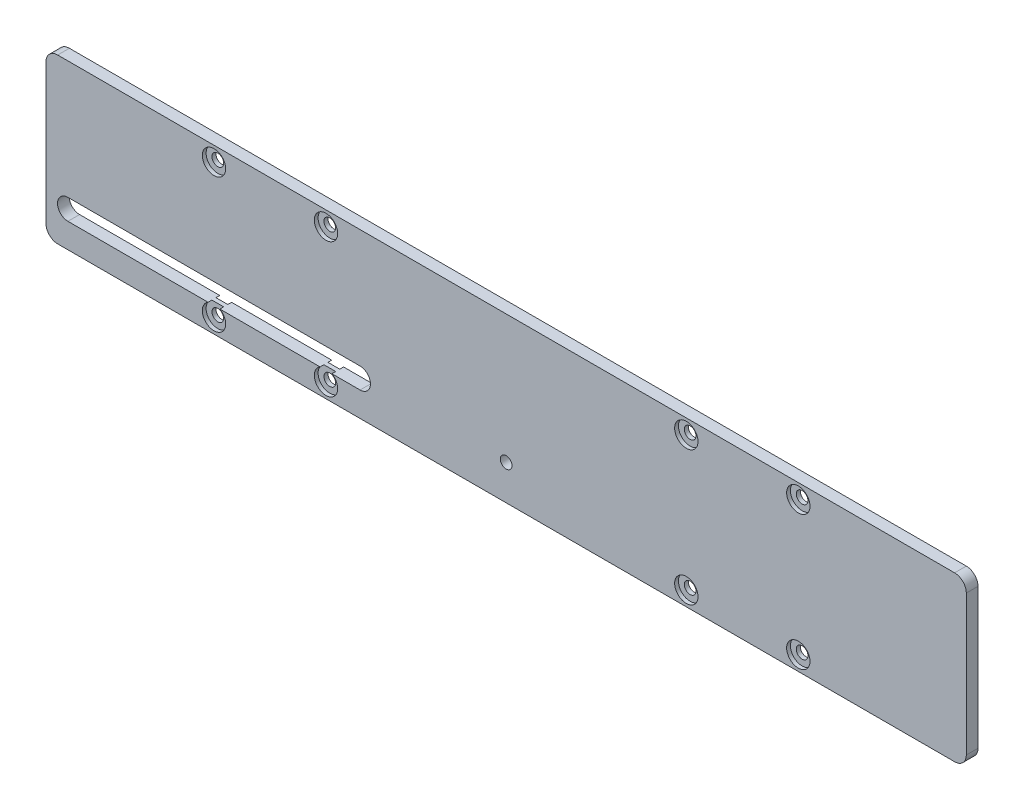
SolidWorks part; units mm, degrees
ref_plane "前视基准面" through (0, 0, 0) normal (0, 0, 1) x (1, 0, 0)
ref_plane "上视基准面" through (0, 0, 0) normal (0, 1, 0) x (1, 0, 0)
ref_plane "右视基准面" through (0, 0, 0) normal (1, 0, 0) x (0, 0, -1)
sketch "草图1" plane through (0, 0, 0) normal (0, 0, 1) x (1, 0, 0)
  line L0 (-150, -16) -> (-50, -16) construction
  line L1 (153.5, -28) -> (-153.5, -28)
  line L2 (157.5, -24) -> (157.5, 24)
  line L3 (153.5, 28) -> (-153.5, 28)
  line L4 (-157.5, -24) -> (-157.5, 24)
  line L5 (157.5, -28) -> (-157.5, 28) construction
  line L6 (157.5, 28) -> (-157.5, -28) construction
  line L7 (-150, -12.45) -> (-50, -12.45)
  line L8 (-150, -19.55) -> (-50, -19.55)
  line L9 (0, 28) -> (0, -28) construction
  arc A0 (157.5, -24) -> (153.5, -28) centre (153.5, -24) cw
  arc A1 (157.5, 24) -> (153.5, 28) centre (153.5, 24) ccw
  arc A2 (-157.5, -24) -> (-153.5, -28) centre (-153.5, -24) ccw
  arc A3 (-157.5, 24) -> (-153.5, 28) centre (-153.5, 24) cw
  arc A4 (-150, -12.45) -> (-150, -19.55) centre (-150, -16) ccw
  arc A5 (-50, -19.55) -> (-50, -12.45) centre (-50, -16) ccw
  circle A7 centre (-100, 23) radius 2
  circle A8 centre (-61.67, 23) radius 2
  circle A9 centre (-100, -23) radius 2
  circle A11 centre (-61.67, -23) radius 2
  circle A12 centre (100, -23) radius 2
  circle A13 centre (61.67, -23) radius 2
  circle A14 centre (61.67, 23) radius 2
  circle A15 centre (100, 23) radius 2
  point P0 (0, 0)
  point P20 (-100, -16)
  dimension "D3" = 4
  dimension "D5" = 7.5
  dimension "D6" = 3.55
  dimension "D7" = 46
  dimension "D8" = 5
  dimension "D9" = 12
  dimension "D10" = 4
  dimension "D11" = 4
  dimension "D12" = 4
  dimension "D13" = 4
  dimension "D14" = 38.33
  dimension "D15" = 38.33
  dimension "D16" = 46
  dimension "D17" = 5
  dimension "D18" = 5
  dimension "D19" = 100
  dimension "D20" = 12
  dimension "D1" = 315
  dimension "D2" = 56
  dimension "D4" = 100
extrude "凸台-拉伸1" add sketch "草图1" along normal blind 4
sketch "草图2" plane through (0, 0, 4) normal (0, 0, 1) x (1, 0, 0)
  line L0 (0, 28) -> (0, -28) construction
  line L1 (153.5, 28) -> (-153.5, 28) construction
  line L2 (-153.5, -28) -> (153.5, -28) construction
  circle A0 centre (-100, 23) radius 4
  circle A1 centre (-61.67, 23) radius 4
  circle A2 centre (-100, -23) radius 4
  circle A3 centre (-61.67, -23) radius 4
  circle A4 centre (61.67, -23) radius 4
  circle A5 centre (100, -23) radius 4
  circle A6 centre (61.67, 23) radius 4
  circle A7 centre (100, 23) radius 4
  dimension "D1" = 8
  dimension "D2" = 8
  dimension "D3" = 8
  dimension "D4" = 8
extrude "切除-拉伸1" cut sketch "草图2" against normal blind 1.3
sketch "草图3" plane through (0, 0, 4) normal (0, 0, 1) x (1, 0, 0)
  line L0 (-153.5, -28) -> (153.5, -28) construction
  circle A2 centre (0, -16) radius 2
  arc A3 (-150, -12.45) -> (-150, -19.55) centre (-150, -16) ccw construction
  dimension "D1" = 12
  dimension "D2" = 150
extrude "切除-拉伸2" cut sketch "草图3" against normal blind 10
sketch "草图5" plane through (0, 0, 0) normal (0, 0, -1) x (-1, 0, 0)
  circle A0 centre (-100, -23) radius 4
  circle A1 centre (-61.67, -23) radius 4
  circle A2 centre (61.67, -23) radius 4
  circle A3 centre (100, -23) radius 4
  circle A4 centre (100, 23) radius 4
  circle A5 centre (61.67, 23) radius 4
  circle A6 centre (-61.67, 23) radius 4
  circle A7 centre (-100, 23) radius 4
extrude "切除-拉伸4" cut sketch "草图5" against normal blind 1.3
